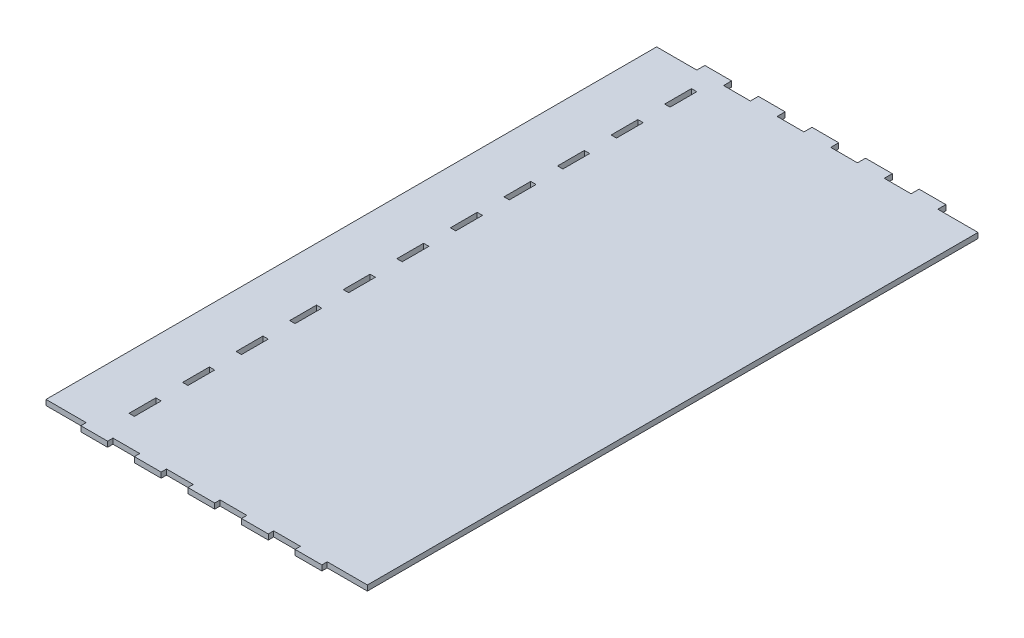
SolidWorks part; units mm, degrees
material "Verre"
ref_plane "Front Plane" through (0, 0, 0) normal (0, 0, 1) x (1, 0, 0)
ref_plane "Top Plane" through (0, 0, 0) normal (0, 1, 0) x (1, 0, 0)
ref_plane "Right Plane" through (0, 0, 0) normal (1, 0, 0) x (0, 0, -1)
sketch "Sketch1" plane through (0, 0, 0) normal (0, 1, 0) x (1, 0, 0)
  line L1 (0, 0) -> (120, 0)
  line L2 (0, 0) -> (0, 227)
  line L3 (0, 227) -> (120, 227)
  line L4 (120, 0) -> (120, 227)
  dimension "D1" = 120
  dimension "D2" = 227
extrude "Boss-Extrude1" add sketch "Sketch1" along normal blind 2
sketch "Sketch2" plane through (0, 0, 0) normal (0, 0, 1) x (1, 0, 0)
  line L0 (0, 0) -> (120, 0) construction
  line L1 (15, 0) -> (25, 0)
  line L2 (15, 0) -> (15, 2)
  line L3 (15, 2) -> (25, 2)
  line L4 (25, 0) -> (25, 2)
  line L5 (0, 2) -> (120, 2) construction
  line L6 (0, 2) -> (0, 0) construction
  dimension "D1" = 10
  dimension "D2" = 15
extrude "Boss-Extrude2" add sketch "Sketch2" along normal blind 3
pattern_linear "LPattern1" count 5 spacing 20 along (1, 0, 0) of "Boss-Extrude2"
sketch "Sketch3" plane through (0, 0, -227) normal (0, 0, -1) x (-1, 0, 0)
  line L0 (-120, 0) -> (0, 0) construction
  line L1 (-95, 0) -> (-105, 0)
  line L2 (-95, 0) -> (-95, 2)
  line L3 (-95, 2) -> (-105, 2)
  line L4 (-105, 0) -> (-105, 2)
  line L5 (-120, 2) -> (0, 2) construction
  line L7 (-120, 2) -> (-120, 0) construction
  dimension "D1" = 15
  dimension "D2" = 10
extrude "Boss-Extrude3" add sketch "Sketch3" along normal blind 3
pattern_linear "LPattern2" count 5 spacing 20 along (-1, 0, 0) of "Boss-Extrude3"
sketch "Sketch4" plane through (0, 2, 0) normal (0, 1, 0) x (1, 0, 0)
  line L0 (0, 0) -> (15, 0) construction
  line L1 (20, 10) -> (23, 10)
  line L2 (20, 10) -> (20, 20)
  line L3 (20, 20) -> (23, 20)
  line L4 (23, 10) -> (23, 20)
  line L5 (0, 227) -> (0, 0) construction
  dimension "D1" = 10
  dimension "D2" = 10
  dimension "D3" = 3
  dimension "D4" = 20
extrude "Cut-Extrude1" cut sketch "Sketch4" against normal through all
pattern_linear "LPattern3" count 11 spacing 20 along (0, 0, -1) of "Cut-Extrude1"
sketch "Esquisse1" plane through (0, 2, 0) normal (0, 1, 0) x (1, 0, 0)
  line L0 (20, 10) -> (23, 10) construction
  line L1 (23, 220) -> (22, 220)
  line L2 (23, 220) -> (23, 10)
  line L3 (23, 10) -> (22, 10)
  line L4 (22, 220) -> (22, 10)
  dimension "D1" = 1
extrude "Boss.-Extru.1" add sketch "Esquisse1" against normal blind 2
sketch "Esquisse2" plane through (0, 0, 0) normal (0, -1, 0) x (1, 0, 0)
  line L1 (120, 0) -> (0, 0)
  line L2 (120, 0) -> (120, 1)
  line L3 (120, 1) -> (0, 1)
  line L4 (0, 0) -> (0, 1)
  dimension "D1" = 1
extrude "Boss.-Extru.2" add sketch "Esquisse2" against normal blind 2
